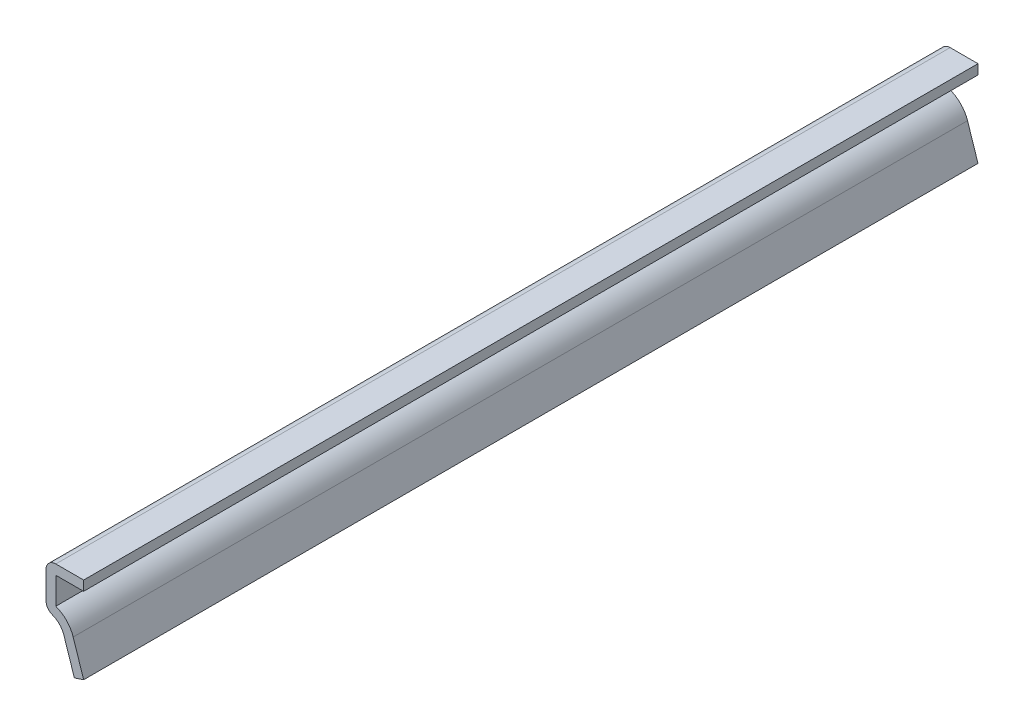
SolidWorks part; units mm, degrees
ref_plane "Front Plane" through (0, 0, 0) normal (0, 0, 1) x (1, 0, 0)
ref_plane "Top Plane" through (0, 0, 0) normal (0, 1, 0) x (1, 0, 0)
ref_plane "Right Plane" through (0, 0, 0) normal (1, 0, 0) x (0, 0, -1)
sketch "Sketch1" plane through (0, 0, 0) normal (0, 0, 1) x (1, 0, 0)
  line L0 (0, 0) -> (0, 15.0812) construction
  line L1 (0, 15.0812) -> (-6.35, 15.0812)
  line L2 (-6.35, 15.0812) -> (-6.35, 7.5406)
  line L3 (-3.3346, 5.3595) -> (-1.568, 0)
  line L4 (-6.35, 7.5406) -> (-2.8425, 7.5406) construction
  line L5 (0, 13.4302) -> (-4.699, 13.4302) construction
  line L6 (-4.699, 13.4302) -> (-4.699, 8.9004) construction
  line L7 (-1.7666, 5.8764) -> (0, 0.5168) construction
  line L8 (-3.3346, 5.3595) -> (-1.5601, -0.0239) construction
  line L9 (-1.7666, 5.8764) -> (0.0079, 0.4929) construction
  line L10 (-1.568, 0) -> (-0.2588, 0.4315) construction
  arc A0 (-6.35, 7.5406) -> (-3.3346, 5.3595) centre (-6.35, 4.3656) cw
  arc A1 (-4.699, 8.9004) -> (-1.7666, 5.8764) centre (-6.35, 4.3656) cw construction
  arc A2 (-6.35, 7.5406) -> (-3.3346, 5.3595) centre (-6.35, 4.3656) cw construction
  point P5 (0, 0)
  point P7 (1.001, 0.832)
  point P16 (0.8544, 0.967)
  point P18 (0.6007, 0.8655)
  point P20 (-3.3947, 4.7315)
  point P22 (0, 0)
  point P24 (0, 7.5406)
  point P25 (-1.7666, 0)
  dimension "D4" = 3.175
  dimension "D1" = 6.35
  dimension "D2" = 1.651
  dimension "D3" = 15.0812
extrude "Extrude-Thin1" add sketch "Sketch1" against normal blind 150.8125 thin contours L1 L2 A0 L3 thin type one direction reverse wall 1.651
fillet "Fillet1" radius 1.651 2 edges at (-6.35, 7.5406, -75.4062) (-6.35, 15.0812, -75.4062)
